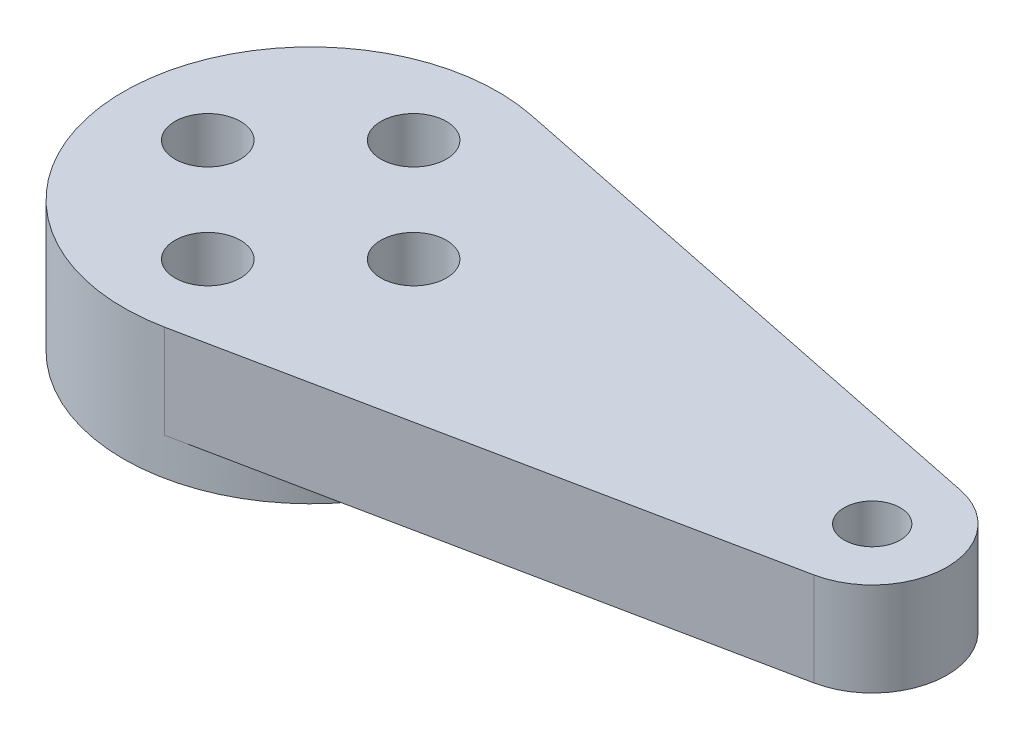
SolidWorks part; units mm, degrees
ref_plane "Front Plane" through (0, 0, 0) normal (0, 0, 1) x (1, 0, 0)
ref_plane "Top Plane" through (0, 0, 0) normal (0, 1, 0) x (1, 0, 0)
ref_plane "Right Plane" through (0, 0, 0) normal (1, 0, 0) x (0, 0, -1)
sketch "Sketch1" plane through (0, 0, 0) normal (0, 1, 0) x (1, 0, 0)
  circle A0 centre (0, 0) radius 10
  circle A1 centre (0, 5.5) radius 1.75
  circle A2 centre (5.5, 0) radius 1.75
  circle A3 centre (0, -5.5) radius 1.75
  circle A4 centre (-5.5, 0) radius 1.75
  point P14 (0, 0)
  dimension "D1" = 20
  dimension "D3" = 3.5
  dimension "D2" = 5.5
  dimension "D4" = 4
extrude "Boss-Extrude1" add sketch "Sketch1" along normal blind 7
sketch "Sketch2" plane through (0, 7, 0) normal (0, 1, 0) x (1, 0, 0)
  line L0 (2, 9.798) -> (30.8, 3.9192)
  line L1 (2, -9.798) -> (30.8, -3.9192)
  circle A0 centre (0, 0) radius 10 construction
  arc A1 (2, -9.798) -> (2, 9.798) centre (0, 0) ccw
  circle A2 centre (30, 0) radius 1.5
  arc A3 (30.8, -3.9192) -> (30.8, 3.9192) centre (30, 0) ccw
  point P8 (0, 0)
  dimension "D1" = 3
  dimension "D2" = 8
  dimension "D3" = 30
extrude "Boss-Extrude2" add sketch "Sketch2" against normal blind 5
